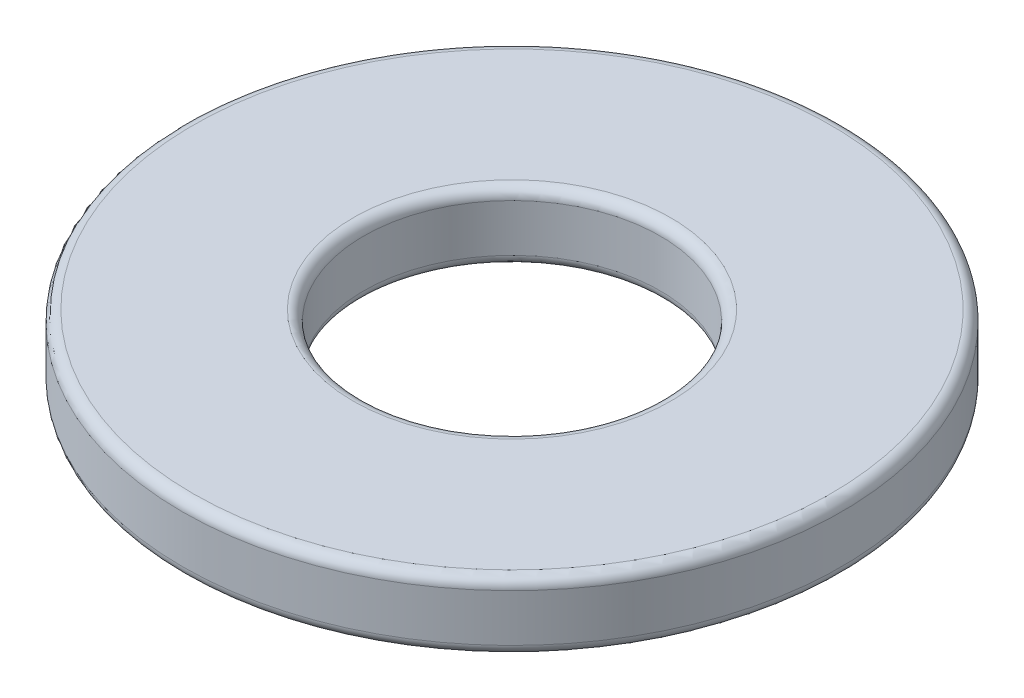
SolidWorks part; units mm, degrees
ref_plane "Front" through (0, 0, 0) normal (0, 0, 1) x (1, 0, 0)
ref_plane "Top" through (0, 0, 0) normal (0, 1, 0) x (1, 0, 0)
ref_plane "Right" through (0, 0, 0) normal (1, 0, 0) x (0, 0, -1)
sketch "Sketch1" plane through (0, 0, 0) normal (0, 1, 0) x (1, 0, 0)
  circle A0 centre (0, 0) radius 7.9375
  circle A1 centre (0, 0) radius 3.5719
  dimension "D1" = 15.875
  dimension "D2" = 7.1437
extrude "Extrude1" add sketch "Sketch1" along normal blind 1.651
fillet "Fillet1" radius 0.254 4 edges at (0, 0, 3.5719) (0, 0, 7.9375) (0, 1.651, 3.5719) (0, 1.651, 7.9375)
